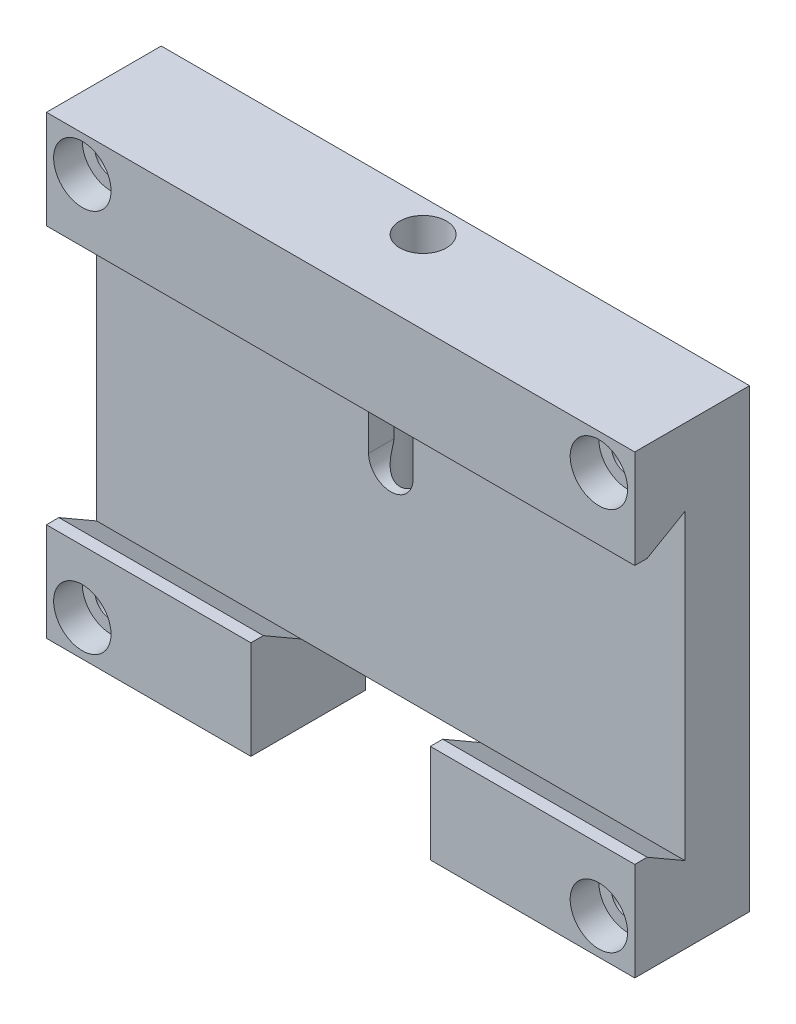
SolidWorks part; units mm, degrees
material "Сплав 2024"
ref_plane "Спереди" through (0, 0, 0) normal (0, 0, 1) x (1, 0, 0)
ref_plane "Сверху" through (0, 0, 0) normal (0, 1, 0) x (1, 0, 0)
ref_plane "Справа" through (0, 0, 0) normal (1, 0, 0) x (0, 0, -1)
sketch "Эскиз1" plane through (0, 0, 0) normal (0, 0, 1) x (1, 0, 0)
  line L1 (0, 0) -> (82, 0)
  line L2 (0, 0) -> (0, -63.5)
  line L3 (0, -63.5) -> (82, -63.5)
  line L4 (82, 0) -> (82, -63.5)
  dimension "D1" = 63.5
  dimension "D2" = 82
extrude "Бобышка-Вытянуть1" add sketch "Эскиз1" along normal blind 16
sketch "Эскиз2" plane through (0, 0, 0) normal (-1, 0, 0) x (0, 0, 1)
  line L0 (0, -31.75) -> (12.8711, -31.75) construction
  line L1 (0, 0) -> (0, -63.5) construction
  line L3 (16, 0) -> (16, -63.5) construction
  line L4 (9, -10.67) -> (16, -14.7115)
  line L5 (9, -10.67) -> (9, -52.83)
  line L6 (9, -52.83) -> (16, -48.7885)
  line L7 (16, -14.7115) -> (16, -48.7885)
  line L8 (9, -10.67) -> (16, -48.7885) construction
  line L9 (9, -52.83) -> (16, -14.7115) construction
  dimension "D1" = 42.16
  dimension "D2" = 60
  dimension "D3" = 60
  dimension "D4" = 7
extrude "Вырез-Вытянуть1" cut sketch "Эскиз2" against normal through all
ref_plane "Плоскость1" through (0, 0, 4) normal (0, 0, 1) x (1, 0, 0)
sketch "Эскиз3" plane through (0, 0, 4) normal (0, 0, 1) x (1, 0, 0)
  line L0 (0, -31.75) -> (82, -31.75) construction
  line L1 (0, -10.67) -> (0, -52.83) construction
  line L2 (82, -10.67) -> (82, -52.83) construction
  line L3 (41, 0) -> (41, -63.5) construction
  line L4 (82, 0) -> (0, 0) construction
  line L5 (0, -63.5) -> (82, -63.5) construction
  line L7 (41, -27.75) -> (82, -27.75)
  line L9 (41, -35.75) -> (82, -35.75)
  line L10 (82, -27.75) -> (82, -35.75)
  line L11 (41, -27.75) -> (82, -35.75) construction
  line L12 (41, -35.75) -> (82, -27.75) construction
  arc A0 (41, -27.75) -> (41, -35.75) centre (41, -31.75) ccw
  point P14 (61.5, -31.75)
  dimension "D1" = 8
sketch "Эскиз5" plane through (0, 0, 9) normal (0, 0, 1) x (1, 0, 0)
  line L0 (0, -31.75) -> (82, -31.75) construction
  line L1 (0, -31.75) -> (82, -31.75) construction
  line L2 (41, 0) -> (41, -63.5) construction
  line L3 (41, 0) -> (41, -63.5) construction
  line L4 (82, -10.67) -> (82, -52.83) construction
  line L5 (33, -27.75) -> (82, -27.75)
  line L7 (33, -35.75) -> (82, -35.75)
  line L8 (82, -27.75) -> (82, -35.75)
  line L9 (33, -27.75) -> (82, -35.75) construction
  line L10 (33, -35.75) -> (82, -27.75) construction
  arc A0 (33, -27.75) -> (33, -35.75) centre (33, -31.75) ccw
  point P6 (57.5, -31.75)
  dimension "D1" = 8
  dimension "D2" = 8
loft "Вырез-По сечениям1" [suppressed] cut profiles "Эскиз5", "Эскиз3"
sketch "Эскиз7" [suppressed] plane through (0, 0, 5) normal (0, 0, 1) x (1, 0, 0)
  line L0 (47.625, 0) -> (47.625, -63.5) construction
  line L1 (95.25, 0) -> (0, 0) construction
  line L2 (0, -63.5) -> (95.25, -63.5) construction
  line L3 (0, -31.75) -> (95.25, -31.75) construction
  line L4 (0, -13.2859) -> (0, -50.2141) construction
  line L5 (95.25, -35.75) -> (95.25, -27.75) construction
  line L6 (67.625, -24.8895) -> (67.625, -40.2612) construction
  line L7 (87.625, -24.8895) -> (87.625, -40.2612) construction
  line L8 (7.625, -24.8895) -> (7.625, -40.2612) construction
  line L9 (27.625, -24.8895) -> (27.625, -40.2612) construction
  circle A0 centre (27.625, -31.75) radius 4
  point P20 (27.625, -31.75)
  dimension "D3" = 8
  dimension "D1" = 20
  dimension "D2" = 20
extrude "Вырез-Вытянуть2" [suppressed] cut sketch "Эскиз7" along normal blind 5
hole_wizard "Отверстие обработанное метчиком M8x1.01" [suppressed] positions "Эскиз9" profile "Эскиз8" tap size "M8x1.0" standard "Ansi Metric"
sketch "Эскиз9" [suppressed] plane through (0, 0, 10) normal (0, 0, 1) x (1, 0, 0)
  line L0 (0, -31.75) -> (95.25, -31.75) construction
  line L1 (7.625, -24.8895) -> (7.625, -40.2612) construction
  line L2 (47.625, 0) -> (47.625, -63.5) construction
  line L3 (67.625, -24.8895) -> (67.625, -40.2612) construction
  line L4 (87.625, -24.8895) -> (87.625, -40.2612) construction
  point P0 (7.625, -31.75)
  point P2 (47.625, -31.75)
  point P4 (67.625, -31.75)
  point P6 (87.625, -31.75)
sketch "Эскиз8" plane through (7.625, -31.75, 10) normal (1, 0, 0) x (0, -1, 0)
  line L0 (0, 0) -> (0, 10)
  line L1 (0, 10) -> (3.5, 10)
  line L2 (3.5, 10) -> (3.5, 0)
  line L5 (3.5, 0) -> (0, 0)
  line L11 (0, -6.35) -> (0, 107.95) construction
  dimension "Диаметр проходного сверла" = 7
  dimension "Глубина проходного сверла" = 10
cosmetic thread "Отверстие резьбы1" [suppressed] parameters "D2"=8
cosmetic thread "Отверстие резьбы2" [suppressed] parameters "D2"=8
cosmetic thread "Отверстие резьбы3" [suppressed] parameters "D2"=8
cosmetic thread "Отверстие резьбы4" [suppressed] parameters "D2"=8
sketch "Эскиз10" [suppressed] plane through (0, 0, 10) normal (0, 0, 1) x (1, 0, 0)
  line L0 (90.25, -35.75) -> (95.25, -35.75)
  line L1 (95.25, -13.2859) -> (95.25, -27.75) construction
  line L2 (95.25, -27.75) -> (39.625, -27.75) construction
  line L3 (90.25, -27.75) -> (95.25, -27.75)
  line L4 (95.25, -27.75) -> (95.25, -22.75)
  line L5 (0, -31.75) -> (95.25, -31.75) construction
  line L6 (0, -31.75) -> (95.25, -31.75) construction
  line L7 (95.25, -35.75) -> (95.25, -40.75)
  arc A0 (90.25, -27.75) -> (95.25, -22.75) centre (90.25, -22.75) ccw
  arc A1 (90.25, -35.75) -> (95.25, -40.75) centre (90.25, -40.75) cw
  dimension "D1" = 5
  dimension "D2" = 5
extrude "Вырез-Вытянуть3" [suppressed] cut sketch "Эскиз10" against normal up to surface (5 mm away)
sketch "Эскиз11" plane through (0, 0, 0) normal (0, 0, -1) x (-1, 0, 0)
  line L0 (-82, -5) -> (0, -5) construction
  line L1 (-82, -63.5) -> (-82, 0) construction
  line L2 (0, 0) -> (0, -63.5) construction
  line L3 (-82, -58.5) -> (0, -58.5) construction
  line L4 (-82, 0) -> (0, 0) construction
  line L5 (0, -63.5) -> (-82, -63.5) construction
  line L8 (-82, -31.75) -> (0, -31.75) construction
  line L9 (-41, 0) -> (-41, -63.5) construction
  line L10 (-77, 0) -> (-77, -63.5) construction
  line L11 (-63.5, -11.75) -> (-18.5, -11.75) construction
  line L12 (-63.5, -11.75) -> (-63.5, -51.75) construction
  line L13 (-63.5, -51.75) -> (-18.5, -51.75) construction
  line L14 (-18.5, -11.75) -> (-18.5, -51.75) construction
  line L15 (-63.5, -11.75) -> (-18.5, -51.75) construction
  line L16 (-63.5, -51.75) -> (-18.5, -11.75) construction
  line L17 (-82, 0) -> (0, 0) construction
  line L18 (-82, -10.67) -> (-82, -52.83) construction
  line L19 (-5, 0) -> (-5, -63.5) construction
  line L20 (0, -10.67) -> (0, -52.83) construction
  line L21 (0, -63.5) -> (-82, -63.5) construction
  point P20 (-41, -31.75)
  dimension "D1" = 5
  dimension "D2" = 5
  dimension "D3" = 5
  dimension "D4" = 5
  dimension "D5" = 45
  dimension "D6" = 40
hole_wizard "Отверстие обработанное метчиком M4x0.71" [suppressed] positions "Эскиз13" profile "Эскиз12" tap size "M4x0.7" standard "Ansi Metric"
sketch "Эскиз13" plane through (0, 0, 0) normal (0, 0, -1) x (-1, 0, 0)
  line L0 (-80, -7) -> (0, -7) construction
  line L1 (-65, 0) -> (-65, -63.5) construction
  line L2 (-15, 0) -> (-15, -63.5) construction
  line L3 (-80, -56.5) -> (0, -56.5) construction
  point P0 (-65, -7)
  point P6 (-15, -7)
  point P10 (-15, -56.5)
  point P14 (-65, -56.5)
sketch "Эскиз12" plane through (65, -7, 0) normal (1, 0, 0) x (0, 1, 0)
  line L0 (0, 0) -> (0, 16)
  line L1 (0, 16) -> (1.65, 16)
  line L2 (1.65, 16) -> (1.65, 0)
  line L5 (1.65, 0) -> (0, 0)
  line L11 (0, -6.35) -> (0, 107.95) construction
  dimension "Диаметр проходного сверла" = 3.3
  dimension "Глубина проходного сверла" = 16
cosmetic thread "Отверстие резьбы5" [suppressed] parameters "D2"=4
cosmetic thread "Отверстие резьбы6" [suppressed] parameters "D2"=4
cosmetic thread "Отверстие резьбы7" [suppressed] parameters "D2"=4
cosmetic thread "Отверстие резьбы8" [suppressed] parameters "D2"=4
sketch "Эскиз15" plane through (0, 0, 16) normal (0, 0, 1) x (1, 0, 0)
  line L0 (41, 0) -> (41, -63.5) construction
  line L1 (82, 0) -> (0, 0) construction
  line L2 (0, -63.5) -> (82, -63.5) construction
  line L3 (82, -48.7885) -> (0, -48.7885) construction
  line L4 (28.5, -48.7885) -> (53.5, -48.7885)
  line L5 (28.5, -48.7885) -> (28.5, -63.5)
  line L6 (28.5, -63.5) -> (53.5, -63.5)
  line L7 (53.5, -48.7885) -> (53.5, -63.5)
  line L8 (28.5, -48.7885) -> (53.5, -63.5) construction
  line L9 (28.5, -63.5) -> (53.5, -48.7885) construction
  point P6 (41, -56.1443)
  dimension "D1" = 25
extrude "Вырез-Вытянуть4" cut sketch "Эскиз15" against normal up to surface (7 mm away) up to face at (41, -31.75, 9)
sketch "Эскиз16" plane through (0, 0, 9) normal (0, 0, 1) x (1, 0, 0)
  line L0 (41, 0) -> (41, -63.5) construction
  line L1 (28.5, -52.83) -> (53.5, -52.83)
  line L2 (28.5, -52.83) -> (28.5, -63.5)
  line L3 (28.5, -63.5) -> (53.5, -63.5)
  line L4 (53.5, -52.83) -> (53.5, -63.5)
  line L5 (28.5, -52.83) -> (53.5, -63.5) construction
  line L6 (28.5, -63.5) -> (53.5, -52.83) construction
  line L7 (28.5, -63.5) -> (53.5, -63.5) construction
  line L8 (82, -52.83) -> (53.5, -52.83) construction
  line L9 (53.5, -63.5) -> (53.5, -52.83) construction
  point P0 (41, -58.165)
extrude "Вырез-Вытянуть5" cut sketch "Эскиз16" against normal up to surface (9 mm away) up to face at (41, -31.75, 0)
sketch "Эскиз17" plane through (0, -52.83, 0) normal (0, -1, 0) x (1, 0, 0)
  line L0 (35.125, 5) -> (60.125, 5) construction
  line L3 (41, 9) -> (41, 0) construction
  line L4 (82, 9) -> (0, 9) construction
  line L5 (28.5, 0) -> (53.5, 0) construction
  circle A0 centre (33.5, 5) radius 2.5
  circle A1 centre (48.5, 5) radius 2.5
  dimension "D1" = 5
  dimension "D2" = 7.5
  dimension "D3" = 5
extrude "Вырез-Вытянуть6" cut sketch "Эскиз17" against normal blind 4
hole_wizard "Отверстие обработанное метчиком M4x0.72" positions "Эскиз19" profile "Эскиз18" tap size "M4x0.7" standard "Ansi Metric"
sketch "Эскиз19" plane through (0, -52.83, 0) normal (0, -1, 0) x (-1, 0, 0)
  line L0 (-41, -9) -> (-41, 0) construction
  line L1 (-35.125, -5) -> (-60.125, -5) construction
  point P0 (-41, -5)
sketch "Эскиз18" plane through (41, -52.83, 5) normal (1, 0, 0) x (0, 0, -1)
  line L0 (0, 0) -> (0, 10.9914)
  line L1 (0, 10.9914) -> (1.65, 10)
  line L2 (1.65, 10) -> (1.65, 0)
  line L5 (1.65, 0) -> (0, 0)
  line L10 (0, 10.9914) -> (-1.65, 10) construction
  line L11 (0, -6.35) -> (0, 107.95) construction
  dimension "Диаметр сверла" = 3.3
  dimension "Глубина сверла" = 10
  dimension "Угол заточки сверла" = 118
cosmetic thread "Отверстие резьбы9" parameters "D1"=8, "D2"=4
hole_wizard "Отверстие обработанное метчиком 3/8-161" [suppressed] positions "Эскиз21" profile "Эскиз20" tap size "3/8-16" standard "Ansi Inch"
sketch "Эскиз21" plane through (0, 0, 0) normal (0, 0, -1) x (-1, 0, 0)
  point P0 (-70.125, -11.75)
  point P3 (-70.125, -51.75)
  point P6 (-25.125, -51.75)
  point P9 (-25.125, -11.75)
sketch "Эскиз20" plane through (70.125, -11.75, 0) normal (1, 0, 0) x (0, 1, 0)
  line L0 (0, 0) -> (0, 10.3847)
  line L1 (0, 10.3847) -> (3.9687, 8)
  line L2 (3.9687, 8) -> (3.9687, 0)
  line L5 (3.9687, 0) -> (0, 0)
  line L10 (0, 10.3847) -> (-3.9688, 8) construction
  line L11 (0, -6.35) -> (0, 107.95) construction
  dimension "Диаметр сверла" = 7.9375
  dimension "Глубина сверла" = 8
  dimension "Угол заточки сверла" = 118
cosmetic thread "Отверстие резьбы10" [suppressed] parameters "D1"=8, "D2"=9.525
cosmetic thread "Отверстие резьбы11" [suppressed] parameters "D1"=8, "D2"=9.525
cosmetic thread "Отверстие резьбы12" [suppressed] parameters "D1"=8, "D2"=9.525
cosmetic thread "Отверстие резьбы13" [suppressed] parameters "D1"=8, "D2"=9.525
chamfer "Фаска1" [suppressed] distance 4 angle 45
hole_wizard "Отверстие обработанное метчиком 1/4-201" [suppressed] positions "Эскиз23" profile "Эскиз22" tap size "1/4-20" standard "Ansi Inch"
sketch "Эскиз23" plane through (0, 0, 0) normal (0, 0, -1) x (-1, 0, 0)
  point P0 (-25.125, -51.75)
  point P3 (-25.125, -11.75)
  point P6 (-70.125, -11.75)
  point P9 (-70.125, -51.75)
sketch "Эскиз22" plane through (25.125, -51.75, 0) normal (1, 0, 0) x (0, 1, 0)
  line L0 (0, 0) -> (0, 10.5338)
  line L1 (0, 10.5338) -> (2.5527, 9)
  line L2 (2.5527, 9) -> (2.5527, 0)
  line L5 (2.5527, 0) -> (0, 0)
  line L10 (0, 10.5338) -> (-2.5527, 9) construction
  line L11 (0, -6.35) -> (0, 107.95) construction
  dimension "Диаметр сверла" = 5.1054
  dimension "Глубина сверла" = 9
  dimension "Угол заточки сверла" = 118
cosmetic thread "Отверстие резьбы14" [suppressed] parameters "D1"=9, "D2"=6.35
cosmetic thread "Отверстие резьбы15" [suppressed] parameters "D1"=9, "D2"=6.35
cosmetic thread "Отверстие резьбы16" [suppressed] parameters "D1"=9, "D2"=6.35
cosmetic thread "Отверстие резьбы17" [suppressed] parameters "D1"=9, "D2"=6.35
sketch "Эскиз25" plane through (0, 0, 9) normal (0, 0, 1) x (1, 0, 0)
  line L0 (41, 0) -> (41, -52.83) construction
  line L1 (82, 0) -> (0, 0) construction
  line L2 (53.5, -52.83) -> (28.5, -52.83) construction
  line L3 (41, -18.7115) -> (41, -25.7115) construction
  line L4 (44.1, -18.7115) -> (44.1, -25.7115)
  line L5 (37.9, -18.7115) -> (37.9, -25.7115)
  line L6 (82, -14.7115) -> (0, -14.7115) construction
  arc A0 (44.1, -18.7115) -> (37.9, -18.7115) centre (41, -18.7115) ccw
  arc A1 (37.9, -25.7115) -> (44.1, -25.7115) centre (41, -25.7115) ccw
  point P8 (41, -22.2115)
  dimension "D1" = 3.1
  dimension "D2" = 4
  dimension "D3" = 7
extrude "Вырез-Вытянуть7" cut sketch "Эскиз25" against normal blind 4
sketch "Эскиз26" plane through (0, 0, 0) normal (0, 1, 0) x (1, 0, 0)
  line L0 (0, -9) -> (82, -9) construction
  line L1 (0, -16) -> (0, 0) construction
  line L2 (82, -16) -> (82, 0) construction
  line L4 (82, 0) -> (0, 0) construction
  line L5 (41, 0) -> (41, -16) construction
  line L6 (82, -16) -> (0, -16) construction
  circle A0 centre (41, -4.5) radius 3.25
  dimension "D2" = 6.5
  dimension "D1" = 9
  dimension "D3" = 4.5
extrude "Вырез-Вытянуть8" cut sketch "Эскиз26" against normal blind 38
sketch "Эскиз27" plane through (0, 0, 0) normal (0, 0, -1) x (-1, 0, 0)
  line L0 (-82, 0) -> (0, 0) construction
  line L1 (-82, 0) -> (-72, 0)
  line L2 (-82, 0) -> (-82, -63.5)
  line L3 (-82, -63.5) -> (-72, -63.5)
  line L4 (-72, 0) -> (-72, -63.5)
  line L5 (-53.5, -63.5) -> (-82, -63.5) construction
  line L7 (-41, 0) -> (-41, -63.5) construction
  line L8 (-82, -63.5) -> (-82, 0) construction
  line L9 (0, -63.5) -> (-10, -63.5)
  line L10 (0, 0) -> (0, -63.5)
  line L11 (0, 0) -> (-10, 0)
  line L12 (-10, 0) -> (-10, -63.5)
  dimension "D1" = 10
extrude "Вырез-Вытянуть9" [suppressed] cut sketch "Эскиз27" against normal blind 5
hole_wizard "Цековка для винта с внутренним шестигранником M41" positions "Эскиз29" profile "Эскиз28" counterbore size "M4" standard "Ansi Metric" end condition through all
sketch "Эскиз29" plane through (30.7592, 26.7934, 16) normal (0, 0, -1) x (-1, 0, 0)
  line L0 (-51.2408, -31.7934) -> (30.7592, -31.7934) construction
  line L1 (-46.2408, -26.7934) -> (-46.2408, -90.2934) construction
  line L2 (-51.2408, -85.2934) -> (30.7592, -85.2934) construction
  line L3 (25.7592, -26.7934) -> (25.7592, -90.2934) construction
  point P0 (-46.2408, -31.7934)
  point P6 (-46.2408, -85.2934)
  point P10 (25.7592, -85.2934)
  point P14 (25.7592, -31.7934)
sketch "Эскиз28" plane through (77, -5, 16) normal (1, 0, 0) x (0, -1, 0)
  line L0 (0, 0) -> (0, 16)
  line L1 (0, 16) -> (2.25, 16)
  line L3 (2.25, 16) -> (2.25, 4)
  line L4 (2.25, 4) -> (4, 4)
  line L5 (4, 4) -> (4, 0)
  line L7 (4, 0) -> (0, 0)
  line L11 (0, -6.35) -> (0, 107.95) construction
  dimension "Диаметр сквозного отверстия" = 4.5
  dimension "Глубина сквозного отверстия" = 16
  dimension "Диаметр цековки" = 8
  dimension "Глубина цековки" = 4
chamfer "Фаска2" distance 1 angle 90 3 edges at (67.75, -48.7885, 16) (14.25, -48.7885, 16) (41, -14.7115, 16)
